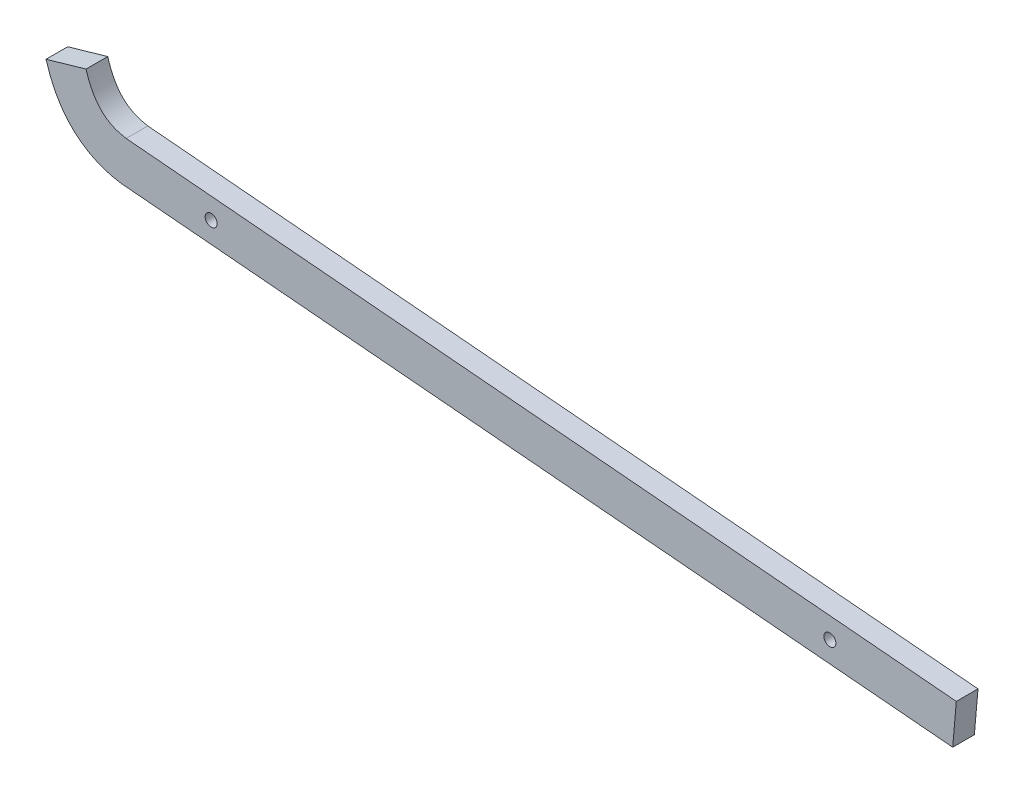
SolidWorks part; units mm, degrees
material "Acrylic (Medium-high impact)"
ref_plane "Front Plane" through (0, 0, 0) normal (0, 0, 1) x (1, 0, 0)
ref_plane "Top Plane" through (0, 0, 0) normal (0, 1, 0) x (1, 0, 0)
ref_plane "Right Plane" through (0, 0, 0) normal (1, 0, 0) x (0, 0, -1)
sketch "Sketch1" plane through (0, 0, 0) normal (0, 0, 1) x (1, 0, 0)
  line L0 (17.559, -16.7495) -> (270.5977, -38.827) construction
  line L1 (16.8231, -23.0594) -> (270.0458, -45.1529)
  line L2 (18.308, -10.4407) -> (271.1496, -32.501)
  line L3 (-6.1009, -1.7612) -> (6.1009, 1.7612)
  line L4 (271.1496, -32.501) -> (270.0458, -45.1529)
  spline S0 degree 2 poles (0, 0) (4.2746, -14.8073) (17.559, -16.7495) knots 0 0 0 1 1 1 construction
  spline S1 degree 1 poles (-6.1009, -1.7612) (16.8231, -23.0594) knots 0 0 1 1 construction
  spline S2 degree 3 poles (-6.1009, -1.7612) (-5.8946, -2.4758) (-5.4427, -3.9058) (-4.4172, -6.6264) (-2.8776, -9.8272) (-0.5911, -13.2966) (3.0656, -17.3628) (7.6032, -20.4242) (12.11, -22.0722) (14.4541, -22.6478) (15.6616, -22.8772) (16.2528, -22.9746) (16.6211, -23.0301) (16.7513, -23.0489) (16.8231, -23.0594) knots 0 0 0 0 0.06293 0.12586 0.251719 0.377579 0.503439 0.755158 0.881017 0.943947 0.975412 0.991145 0.999011 1.006877 1.006877 1.006877 1.006877
  spline S3 degree 1 poles (6.1009, 1.7612) (18.308, -10.4407) knots 0 0 1 1 construction
  spline S4 degree 3 poles (6.1009, 1.7612) (6.244, 1.2654) (6.562, 0.2582) (7.2398, -1.5417) (8.1919, -3.521) (9.4596, -5.4516) (10.8391, -7.0011) (12.3458, -8.2353) (14.0316, -9.2152) (15.6564, -9.8441) (17.1059, -10.2266) (17.9118, -10.3791) (18.308, -10.4407) knots 0 0 0 0 0.061967 0.123935 0.247869 0.371804 0.495739 0.619673 0.743608 0.867543 0.92951 0.991477 0.991477 0.991477 0.991477
  dimension "D1" = 254
  dimension "D2" = 11.0899
  dimension "D3" = 14.7865
  dimension "D4" = 17.559
  dimension "D5" = 153.231
  dimension "D6" = 253.0387
  dimension "D7" = 6.35
  dimension "D8" = 6.35
extrude "Boss-Extrude1" add sketch "Sketch1" along normal blind 6.604
hole_wizard "#6 Clearance Hole1" positions "Sketch2" profile "Sketch3" hole size "#6" standard "ANSI Inch"
sketch "Sketch2" plane through (0, 0, 6.604) normal (0, 0, 1) x (1, 0, 0)
  line L0 (270.5977, -38.827) -> (-37.1249, -11.9783) construction
  line L1 (270.0458, -45.1529) -> (271.1496, -32.501) construction
  line L3 (16.8231, -23.0594) -> (270.0458, -45.1529) construction
  point P9 (44.2009, -19.074)
  point P11 (232.6419, -35.5153)
  point P14 (34.1259, -18.1949)
  dimension "D1" = 38.1
  dimension "D2" = 38.1
sketch "Sketch3" plane through (232.6419, -35.5153, 6.604) normal (1, 0, 0) x (0, -1, 0)
  line L0 (0, 0) -> (0, 11.2589)
  line L1 (0, 11.2589) -> (1.8288, 10.16)
  line L2 (1.8288, 10.16) -> (1.8288, 0)
  line L5 (1.8288, 0) -> (0, 0)
  line L10 (0, 11.2589) -> (-1.8288, 10.16) construction
  line L11 (0, -6.35) -> (0, 107.95) construction
  dimension "Hole Dia." = 3.6576
  dimension "Hole Depth" = 10.16
  dimension "Drill Angle" = 118
